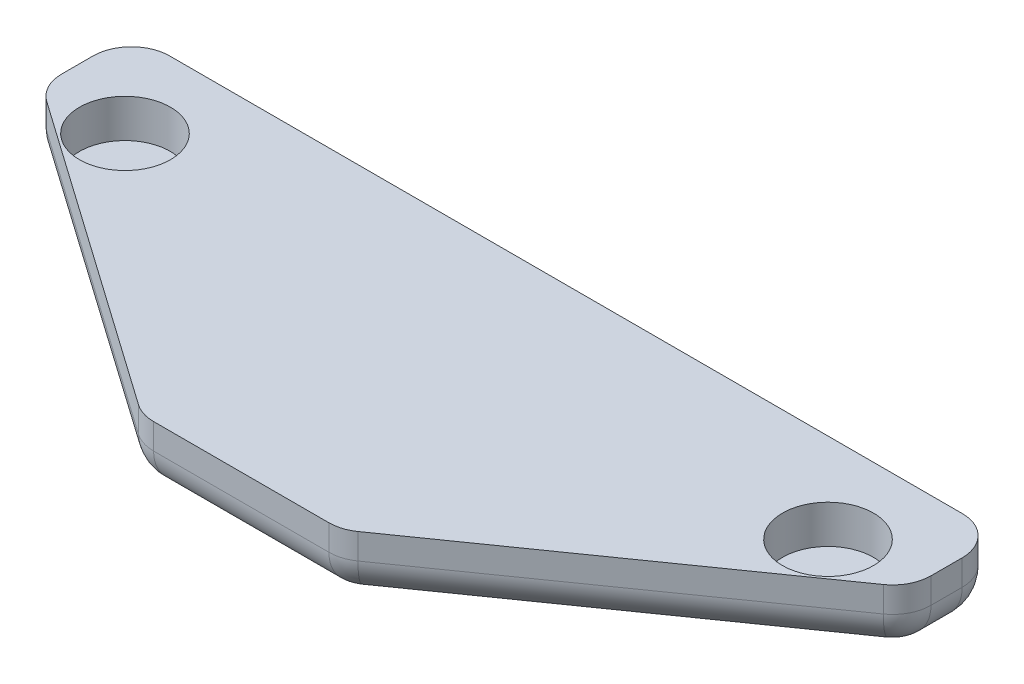
SolidWorks part; units mm, degrees
ref_plane "Front Plane" through (0, 0, 0) normal (0, 0, 1) x (1, 0, 0)
ref_plane "Top Plane" through (0, 0, 0) normal (0, 1, 0) x (1, 0, 0)
ref_plane "Right Plane" through (0, 0, 0) normal (1, 0, 0) x (0, 0, -1)
sketch "Sketch1" plane through (0, 0, 0) normal (0, 1, 0) x (1, 0, 0)
  line L0 (-21.2162, 11.7419) -> (-21.2162, 8.2419)
  line L1 (-21.2162, 8.2419) -> (-8.1205, -0.9581)
  line L2 (-8.1205, -0.9581) -> (-4.2162, -0.9581)
  line L7 (-4.2162, -0.9581) -> (-4.2162, 11.7419)
  line L10 (-4.2162, 11.7419) -> (-21.2162, 11.7419)
  dimension "D1" = 3.9044
  dimension "D2" = 9.2
  dimension "D4" = 17
extrude "Boss-Extrude1" add sketch "Sketch1" along normal blind 2.5
sketch "Sketch2" plane through (0, 2.5, 0) normal (0, 1, 0) x (1, 0, 0)
  line L0 (-17.9662, 11.7419) -> (-17.9662, -0.786) construction
  line L1 (-4.2162, 11.7419) -> (-21.2162, 11.7419) construction
  line L2 (-21.2162, 8.2419) -> (-4.2162, 8.2419) construction
  line L3 (-21.2162, 11.7419) -> (-21.2162, 8.2419) construction
  line L4 (-4.2162, -0.9581) -> (-4.2162, 11.7419) construction
  circle A0 centre (-17.9662, 8.2419) radius 1.78
  dimension "D1" = 3.25
  dimension "D2" = 3.5
extrude "Cut-Extrude1" cut sketch "Sketch2" against normal blind 1.5
fillet "Fillet1" radius 1.5 7 edges at (-8.1205, 1.25, 0.9581) (-21.2162, 1.25, -8.2419) (-21.2162, 1.25, -11.7419) (-6.1683, 0, 0.9581) (-14.6683, 0, -3.6419) (-21.2162, 0, -9.9919) (-12.7162, 0, -11.7419)
mirror "Mirror1" about plane through (-4.2162, 2.5, 0.9581) normal (-1, 0, 0) of bodies 102
